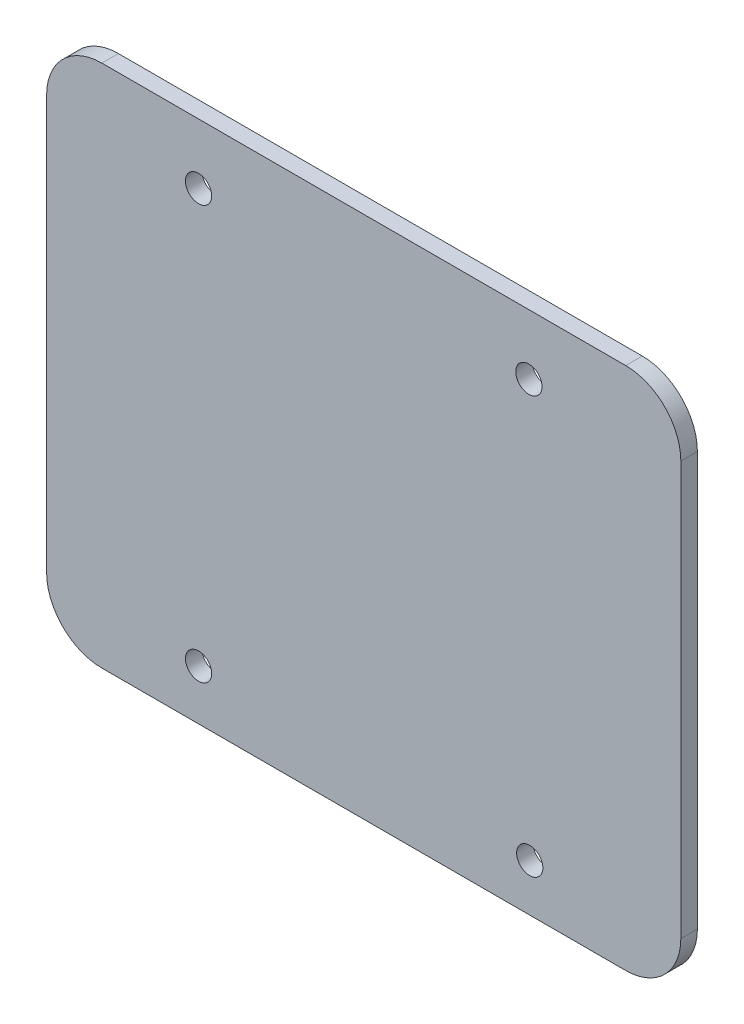
SolidWorks part; units mm, degrees
ref_plane "Alzado" through (0, 0, 0) normal (0, 0, 1) x (1, 0, 0)
ref_plane "Planta" through (0, 0, 0) normal (0, 1, 0) x (1, 0, 0)
ref_plane "Vista lateral" through (0, 0, 0) normal (1, 0, 0) x (0, 0, -1)
sketch "Croquis1" plane through (0, 0, 0) normal (0, 0, 1) x (1, 0, 0)
  line L0 (27.55, 84.08) -> (87.45, 84.08) construction
  line L1 (10, 0) -> (105, 0)
  line L2 (0, 10) -> (0, 85)
  line L3 (10, 95) -> (105, 95)
  line L4 (115, 10) -> (115, 85)
  arc A0 (10, 0) -> (0, 10) centre (10, 10) cw
  arc A1 (105, 0) -> (115, 10) centre (105, 10) ccw
  arc A2 (105, 95) -> (115, 85) centre (105, 85) cw
  arc A3 (0, 85) -> (10, 95) centre (10, 85) cw
  circle A4 centre (27.55, 84.08) radius 2.3813
  circle A5 centre (87.45, 84.08) radius 2.3813
  circle A6 centre (27.55, 9.08) radius 2.3813
  circle A7 centre (87.6, 8.5801) radius 2.3813
  point P7 (0, 0)
  point P10 (115, 0)
  point P13 (115, 95)
  point P16 (0, 95)
  point P34 (57.5, 84.08)
  point P35 (57.5, 95)
  dimension "D3" = 10
  dimension "D4" = 4.7625
  dimension "D8" = 75.5
  dimension "D9" = 60.05
  dimension "D12" = 4.7625
  dimension "D13" = 4.7625
  dimension "D1" = 95
  dimension "D2" = 115
  dimension "D5" = 10.92
  dimension "D6" = 75
  dimension "D7" = 59.9
extrude "Saliente-Extruir1" add sketch "Croquis1" along normal blind 3
